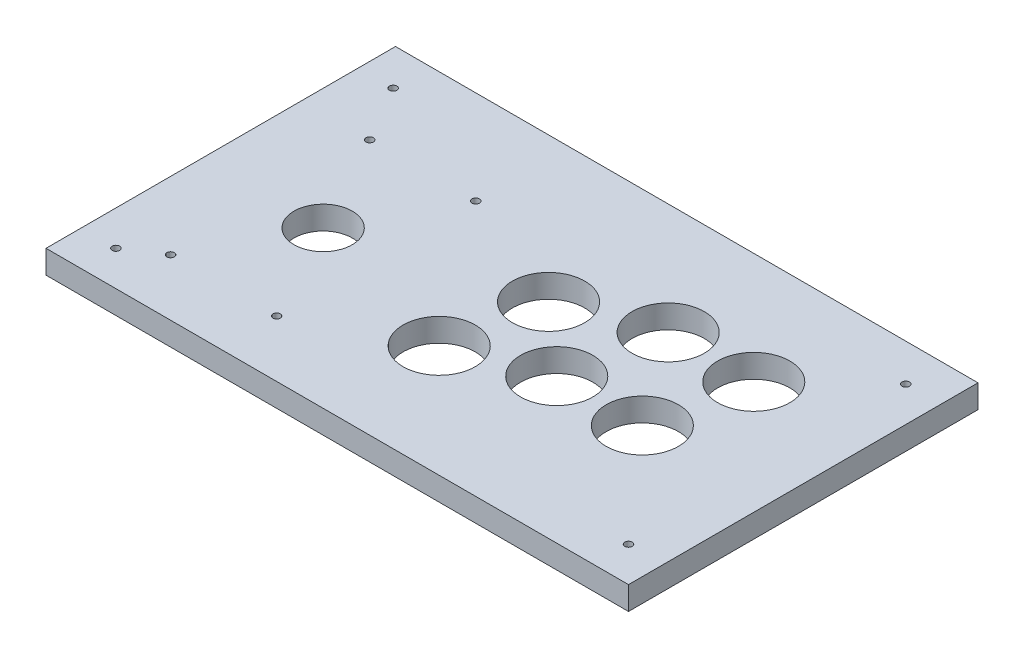
SolidWorks part; units mm, degrees
ref_plane "Alzado" through (0, 0, 0) normal (0, 0, 1) x (1, 0, 0)
ref_plane "Planta" through (0, 0, 0) normal (0, 1, 0) x (1, 0, 0)
ref_plane "Vista lateral" through (0, 0, 0) normal (1, 0, 0) x (0, 0, -1)
sketch "Croquis1" plane through (0, 0, 0) normal (0, 1, 0) x (1, 0, 0)
  line L1 (-125, 75) -> (125, 75)
  line L2 (-125, 75) -> (-125, -75)
  line L3 (-125, -75) -> (125, -75)
  line L4 (125, 75) -> (125, -75)
  line L5 (-125, 75) -> (125, -75) construction
  line L6 (-125, -75) -> (125, 75) construction
  point P0 (0, 0)
  dimension "D1" = 250
  dimension "D2" = 150
extrude "Saliente-Extruir1" add sketch "Croquis1" along normal blind 10
sketch "Croquis2" plane through (0, 10, 0) normal (0, 1, 0) x (1, 0, 0)
  line L0 (-73.1027, 4.5471) -> (-73.1027, -20.4529) construction
  line L1 (2.765, 28.4308) -> (2.765, -2.5692) construction
  line L2 (-4.3708, -11.3783) -> (-4.3708, -42.3783) construction
  line L3 (32.1135, 2.587) -> (32.1135, -28.413) construction
  line L4 (39.7815, 42.7431) -> (39.7815, 11.7431) construction
  line L5 (76.5179, 42.7431) -> (76.5179, 11.7431) construction
  line L6 (68.8513, 2.587) -> (68.8513, -28.413) construction
  circle A0 centre (-73.1027, -7.9529) radius 12.5
  circle A1 centre (-4.3708, -26.8783) radius 15.5
  circle A2 centre (2.765, 12.9308) radius 15.5
  circle A3 centre (39.7815, 27.2431) radius 15.5
  circle A4 centre (76.5179, 27.2431) radius 15.5
  circle A5 centre (68.8513, -12.913) radius 15.5
  circle A6 centre (32.1135, -12.913) radius 15.5
  dimension "D2" = 31
  dimension "D1" = 25
extrude "Cortar-Extruir1" cut sketch "Croquis2" against normal up to next
sketch "Croquis3" plane through (0, 10, 0) normal (0, 1, 0) x (1, 0, 0)
  line L0 (110, -60) -> (125, -60) construction
  line L1 (125, -75) -> (125, 75) construction
  line L2 (-110, -60) -> (-125, -60) construction
  line L3 (-125, 75) -> (-125, -75) construction
  line L4 (-110, -60) -> (-110, -75) construction
  line L5 (-125, -75) -> (125, -75) construction
  line L6 (110, -60) -> (110, -75) construction
  line L7 (110, 59) -> (110, 75) construction
  line L8 (125, 75) -> (-125, 75) construction
  line L9 (110, 59) -> (125, 59) construction
  line L10 (-110, 59) -> (-110, 75) construction
  line L11 (-110, 59) -> (-125, 59) construction
  line L12 (-95.8527, 34.7671) -> (-50.3527, 34.7671) construction
  line L13 (-50.3527, 34.7671) -> (-50.3527, -50.6729) construction
  line L14 (-50.3527, -50.6729) -> (-95.8527, -50.6729) construction
  line L15 (-95.8527, -50.6729) -> (-95.8527, 34.7671) construction
  line L20 (110, -60) -> (110, 59) construction
  line L21 (-110, -60) -> (110, -60) construction
  line L22 (-110, 59) -> (-110, -60) construction
  line L23 (110, 59) -> (-110, 59) construction
  circle A0 centre (-110, 59) radius 1.6
  circle A1 centre (110, 59) radius 1.6
  circle A2 centre (110, -60) radius 1.6
  circle A3 centre (-110, -60) radius 1.6
  circle A6 centre (-50.3527, 34.7671) radius 1.6
  circle A7 centre (-50.3527, -50.6729) radius 1.6
  circle A8 centre (-95.8527, -50.6729) radius 1.6
  circle A9 centre (-95.8527, 34.7671) radius 1.6
  dimension "D2" = 3.2
  dimension "D10" = 3.2
  dimension "D1" = 15
  dimension "D3" = 15
  dimension "D4" = 15
  dimension "D5" = 15
  dimension "D6" = 15
  dimension "D7" = 16
  dimension "D8" = 16
  dimension "D9" = 15
  dimension "D11" = 9.3271
  dimension "D12" = 14.1473
extrude "Cortar-Extruir2" cut sketch "Croquis3" against normal up to next
